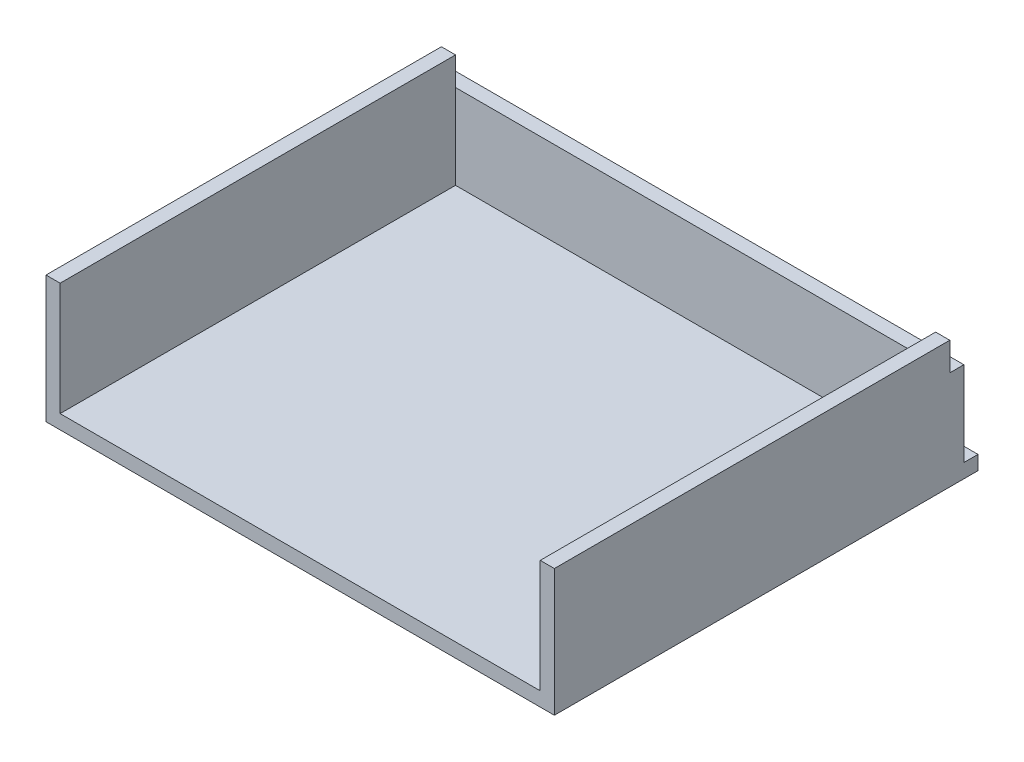
SolidWorks part; units mm, degrees
ref_plane "Front Plane" through (0, 0, 0) normal (0, 0, 1) x (1, 0, 0)
ref_plane "Top Plane" through (0, 0, 0) normal (0, 1, 0) x (1, 0, 0)
ref_plane "Right Plane" through (0, 0, 0) normal (1, 0, 0) x (0, 0, -1)
sketch "Sketch1" plane through (0, 0, 0) normal (0, 1, 0) x (1, 0, 0)
  line L1 (-80.6051, 50.2421) -> (99.3949, 50.2421)
  line L2 (-80.6051, 50.2421) -> (-80.6051, -99.7579)
  line L3 (-80.6051, -99.7579) -> (99.3949, -99.7579)
  line L4 (99.3949, 50.2421) -> (99.3949, -99.7579)
  dimension "D1" = 180
  dimension "D2" = 150
extrude "Boss-Extrude1" add sketch "Sketch1" along normal blind 5
sketch "Sketch5" plane through (0, 0, 99.7579) normal (0, 0, 1) x (1, 0, 0)
  line L1 (-80.6051, 5) -> (-75.6051, 5)
  line L2 (-80.6051, 5) -> (-80.6051, 45)
  line L3 (-80.6051, 45) -> (-75.6051, 45)
  line L4 (-75.6051, 5) -> (-75.6051, 45)
  line L5 (99.3949, 5) -> (94.3949, 5)
  line L6 (99.3949, 5) -> (99.3949, 45)
  line L7 (99.3949, 45) -> (94.3949, 45)
  line L8 (94.3949, 5) -> (94.3949, 45)
  dimension "D1" = 5
  dimension "D2" = 40
  dimension "D3" = 5
  dimension "D4" = 40
extrude "Boss-Extrude2" add sketch "Sketch5" against normal blind 140
sketch "Sketch13" plane through (99.3949, 0, 0) normal (1, 0, 0) x (0, 0, -1)
  line L1 (40.2421, 5) -> (45.2421, 5)
  line L2 (40.2421, 5) -> (40.2421, 35)
  line L3 (40.2421, 35) -> (45.2421, 35)
  line L4 (45.2421, 5) -> (45.2421, 35)
  dimension "D1" = 30
  dimension "D2" = 5
extrude "Boss-Extrude9" add sketch "Sketch13" against normal blind 180
